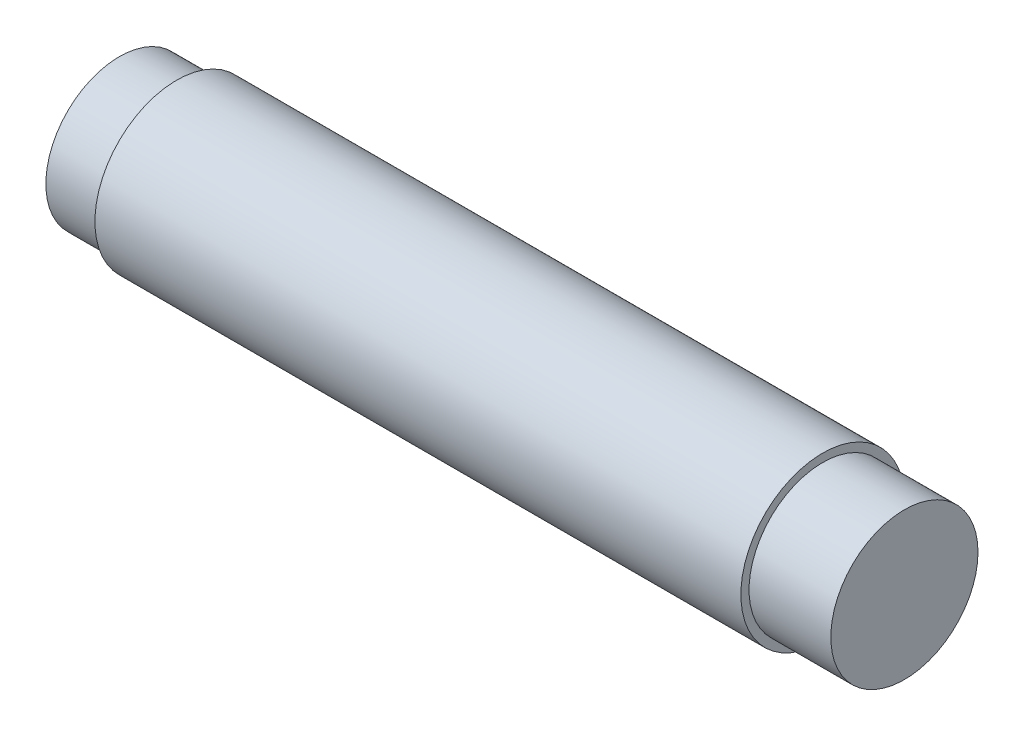
SolidWorks part; units mm, degrees
material "201 Annealed Stainless Steel (SS)"
ref_plane "Front Plane" through (0, 0, 0) normal (0, 0, 1) x (1, 0, 0)
ref_plane "Top Plane" through (0, 0, 0) normal (0, 1, 0) x (1, 0, 0)
ref_plane "Right Plane" through (0, 0, 0) normal (1, 0, 0) x (0, 0, -1)
sketch "Sketch1" plane through (0, 0, 0) normal (1, 0, 0) x (0, 0, -1)
  circle A0 centre (0, 0) radius 5
  dimension "D1" = 10
extrude "Boss-Extrude1" add sketch "Sketch1" along normal blind 19 and the other way blind 20.5
sketch "Sketch2" plane through (19, 0, 0) normal (1, 0, 0) x (0, 0, -1)
  circle A0 centre (0, 0) radius 4.5
  dimension "D1" = 9
extrude "Boss-Extrude2" add sketch "Sketch2" along normal blind 5
mirror "Mirror1" about plane through (0, 0, 0) normal (1, 0, 0) of "Boss-Extrude2"
